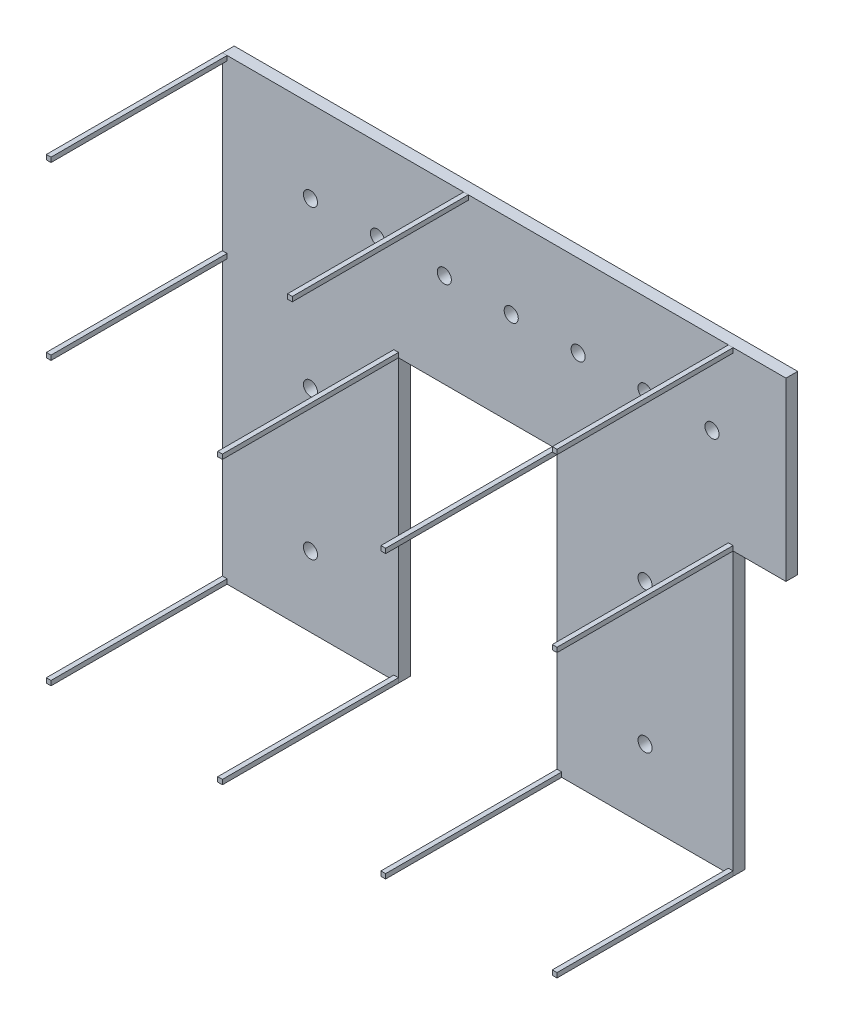
SolidWorks part; units mm, degrees
ref_plane "Front Plane" through (0, 0, 0) normal (0, 0, 1) x (1, 0, 0)
ref_plane "Top Plane" through (0, 0, 0) normal (0, 1, 0) x (1, 0, 0)
ref_plane "Right Plane" through (0, 0, 0) normal (1, 0, 0) x (0, 0, -1)
sketch "Sketch1" plane through (0, 0, 0) normal (0, 0, 1) x (1, 0, 0)
  line L0 (0, 0) -> (0, 3900)
  line L1 (0, 3900) -> (4800, 3900)
  line L2 (4800, 3900) -> (4800, 2400)
  line L3 (4800, 2400) -> (4350, 2400)
  line L4 (4350, 2400) -> (4350, 0)
  line L5 (4350, 0) -> (2850, 0)
  line L6 (2850, 0) -> (2850, 2400)
  line L7 (2850, 2400) -> (1500, 2400)
  line L8 (1500, 2400) -> (1500, 0)
  line L9 (1500, 0) -> (0, 0)
  circle A0 centre (750, 3200) radius 60
  circle A1 centre (1320, 3200) radius 60
  circle A2 centre (1890, 3200) radius 60
  circle A3 centre (2460, 3200) radius 60
  circle A4 centre (3030, 3200) radius 60
  circle A5 centre (3600, 3200) radius 60
  circle A6 centre (4170, 3200) radius 60
  circle A8 centre (750, 1800) radius 60
  circle A9 centre (750, 600) radius 60
  circle A10 centre (3600, 600) radius 60
  circle A11 centre (3600, 1800) radius 60
  dimension "D8" = 750
  dimension "D18" = 120
  dimension "D19" = 120
  dimension "D20" = 120
  dimension "D21" = 120
  dimension "D22" = 120
  dimension "D24" = 450
  dimension "D1" = 2400
  dimension "D2" = 3900
  dimension "D3" = 1350
  dimension "D4" = 1500
  dimension "D5" = 1500
  dimension "D6" = 4800
  dimension "D9" = 7
  dimension "D10" = 600
  dimension "D11" = 600
  dimension "D12" = 750
  dimension "D13" = 750
  dimension "D14" = 750
  dimension "D15" = 750
  dimension "D16" = 600
  dimension "D17" = 600
  dimension "D23" = 700
extrude "Boss-Extrude1" add sketch "Sketch1" along normal blind 100
sketch "Sketch2" plane through (0, 0, 100) normal (0, 0, 1) x (1, 0, 0)
  line L0 (2890, 2400) -> (2850, 2400)
  line L1 (0, 3900) -> (40, 3900)
  line L2 (0, 3900) -> (0, 3860)
  line L3 (0, 3860) -> (40, 3860)
  line L4 (40, 3900) -> (40, 3860)
  line L5 (0, 0) -> (40, 0)
  line L6 (0, 0) -> (0, 40)
  line L7 (0, 40) -> (40, 40)
  line L8 (40, 0) -> (40, 40)
  line L9 (1500, 0) -> (1460, 0)
  line L10 (1500, 0) -> (1500, 40)
  line L11 (1500, 40) -> (1460, 40)
  line L12 (1460, 0) -> (1460, 40)
  line L13 (1500, 2400) -> (1460, 2400)
  line L14 (1500, 2400) -> (1500, 2440)
  line L15 (1500, 2440) -> (1460, 2440)
  line L16 (1460, 2400) -> (1460, 2440)
  line L17 (2890, 2400) -> (2890, 2440)
  line L18 (2890, 2440) -> (2850, 2440)
  line L19 (2850, 2400) -> (2850, 2440)
  line L21 (4350, 0) -> (4310, 0)
  line L22 (4350, 0) -> (4350, 40)
  line L23 (4350, 40) -> (4310, 40)
  line L24 (4310, 0) -> (4310, 40)
  line L25 (2890, 0) -> (2850, 0)
  line L26 (2890, 0) -> (2890, 40)
  line L27 (2890, 40) -> (2850, 40)
  line L28 (2850, 0) -> (2850, 40)
  line L29 (4350, 2400) -> (4310, 2400)
  line L30 (4350, 2400) -> (4350, 2440)
  line L31 (4350, 2440) -> (4310, 2440)
  line L32 (4310, 2400) -> (4310, 2440)
  line L33 (4350, 3860) -> (4310, 3860)
  line L34 (4350, 3860) -> (4350, 3900)
  line L35 (4350, 3900) -> (4310, 3900)
  line L36 (4310, 3860) -> (4310, 3900)
  line L37 (2850, 0) -> (4350, 0) construction
  line L38 (2850, 2400) -> (2850, 0) construction
  line L39 (1500, 2400) -> (2850, 2400) construction
  line L40 (2095, 3860) -> (2055, 3860)
  line L41 (2095, 3860) -> (2095, 3900)
  line L42 (2095, 3900) -> (2055, 3900)
  line L43 (2055, 3860) -> (2055, 3900)
  line L44 (40, 2400) -> (0, 2400)
  line L45 (40, 2400) -> (40, 2440)
  line L46 (40, 2440) -> (0, 2440)
  line L47 (0, 2400) -> (0, 2440)
  line L48 (0, 3900) -> (0, 0) construction
  line L49 (4800, 3900) -> (0, 3900) construction
  line L50 (4350, 2400) -> (4800, 2400) construction
  line M7 (0, 0) -> (1500, 0)
  line M8 (1500, 0) -> (1500, 2400)
  line M9 (1500, 2400) -> (2850, 2400)
  line M10 (2850, 2400) -> (2850, 0)
  line M11 (2850, 0) -> (4350, 0)
  line M12 (4350, 0) -> (4350, 2400)
  line M15 (4800, 3900) -> (0, 3900)
  line M16 (0, 3900) -> (0, 0)
  dimension "D1" = 40
  dimension "D2" = 40
  dimension "D3" = 40
  dimension "D4" = 40
  dimension "D5" = 40
  dimension "D6" = 40
  dimension "D7" = 40
  dimension "D8" = 40
  dimension "D9" = 40
  dimension "D10" = 40
  dimension "D11" = 40
  dimension "D12" = 40
  dimension "D13" = 40
  dimension "D14" = 40
  dimension "D15" = 40
  dimension "D16" = 40
  dimension "D17" = 40
  dimension "D18" = 40
  dimension "D19" = 2015
  dimension "D20" = 40
  dimension "D21" = 40
  dimension "D22" = 40
  dimension "D23" = 40
extrude "Boss-Extrude2" add sketch "Sketch2" along normal blind 1500 separate body contours L8 L7 M7 M16 | L16 L13 L14 L15 | L12 L11 M7 M8 | L24 L23 M11 M12 | L32 L29 L30 L31 | L36 L33 L34 M15 | L43 L40 L41 M15 | L19 L17 L18 M9 | L4 L3 M15 M16 | L45 L46 L44 M16 | L26 L27 M10 M11
ref_plane "Plane1" through (0, 0, 1000) normal (0, 0, 1) x (1, 0, 0)
equation "\"A\"= 40"
equation "\"D9@Sketch2\"=\"A\""
equation "\"D10@Sketch2\"=\"A\""
equation "\"D11@Sketch2\"=\"A\""
equation "\"D12@Sketch2\"=\"A\""
equation "\"D6@Sketch2\"=\"A\""
equation "\"D5@Sketch2\"=\"A\""
equation "\"D4@Sketch2\"=\"A\""
equation "\"D3@Sketch2\"=\"A\""
equation "\"D8@Sketch2\"=\"A\""
equation "\"D7@Sketch2\"=\"A\""
equation "\"D2@Sketch2\"=\"A\""
equation "\"D1@Sketch2\"=\"A\""
equation "\"D13@Sketch2\"=\"A\""
equation "\"D14@Sketch2\"=\"A\""
equation "\"D15@Sketch2\"=\"A\""
equation "\"D16@Sketch2\"=\"A\""
equation "\"D17@Sketch2\"=\"A\""
equation "\"D18@Sketch2\"=\"A\""
equation "\"D\"=120"
equation "\"D18@Sketch1\"=\"D\""
equation "\"D19@Sketch1\"=\"D\""
equation "\"D20@Sketch1\"=\"D\""
equation "\"D21@Sketch1\"=\"D\""
equation "\"D22@Sketch1\"=\"D\""
equation "\"D20@Sketch2\"=\"A\""
equation "\"D21@Sketch2\"=\"A\""
equation "\"D22@Sketch2\"=\"A\""
equation "\"D23@Sketch2\"=\"A\""
equation "\"b\"=750"
equation "\"D12@Sketch1\"=\"b\""
equation "\"D13@Sketch1\"=\"b\""
equation "\"D8@Sketch1\"=\"b\""
